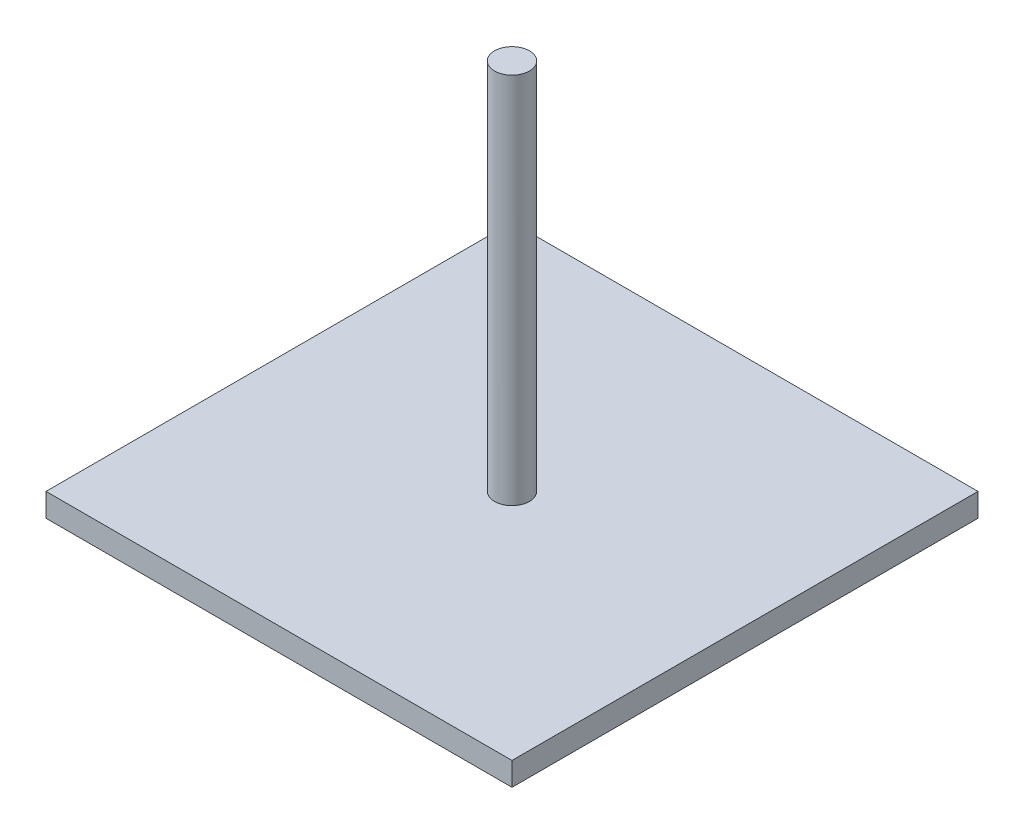
SolidWorks part; units mm, degrees
ref_plane "Front Plane" through (0, 0, 0) normal (0, 0, 1) x (1, 0, 0)
ref_plane "Top Plane" through (0, 0, 0) normal (0, 1, 0) x (1, 0, 0)
ref_plane "Right Plane" through (0, 0, 0) normal (1, 0, 0) x (0, 0, -1)
sketch "Sketch1" plane through (0, 0, 0) normal (0, 1, 0) x (1, 0, 0)
  line L1 (-63.5, -63.5) -> (63.5, -63.5)
  line L2 (-63.5, -63.5) -> (-63.5, 63.5)
  line L3 (-63.5, 63.5) -> (63.5, 63.5)
  line L4 (63.5, -63.5) -> (63.5, 63.5)
  line L5 (-63.5, -63.5) -> (63.5, 63.5) construction
  line L6 (-63.5, 63.5) -> (63.5, -63.5) construction
  point P0 (0, 0)
  dimension "D1" = 127
extrude "Boss-Extrude1" add sketch "Sketch1" along normal blind 6.35
sketch "Sketch2" plane through (0, 6.35, 0) normal (0, 1, 0) x (1, 0, 0)
  circle A0 centre (0, 0) radius 4.7625
  dimension "D1" = 9.525
extrude "Boss-Extrude2" add sketch "Sketch2" along normal blind 101.6
